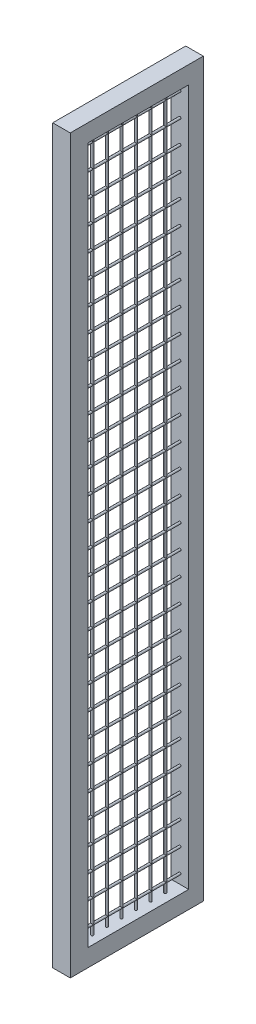
SolidWorks part; units mm, degrees
ref_plane "Piano frontale" through (0, 0, 0) normal (0, 0, 1) x (1, 0, 0)
ref_plane "Piano superiore" through (0, 0, 0) normal (0, 1, 0) x (1, 0, 0)
ref_plane "Piano destro" through (0, 0, 0) normal (1, 0, 0) x (0, 0, -1)
sketch "Schizzo1" plane through (0, 0, 1950) normal (0, 0, -1) x (-1, 0, 0)
  line L0 (-50, 2555) -> (-50, 50) construction
  line L1 (-30, 110) -> (30, 110)
  line L2 (-30, 110) -> (-30, 50)
  line L3 (-30, 50) -> (30, 50)
  line L4 (30, 110) -> (30, 50)
  line L5 (50, 2555) -> (50, 50) construction
  line L6 (-100, 50) -> (100, 50) construction
  line L7 (50, 2555) -> (-50, 2555) construction
  line L8 (-30, 2555) -> (30, 2555)
  line L9 (-30, 2555) -> (-30, 2495)
  line L10 (-30, 2495) -> (30, 2495)
  line L11 (30, 2555) -> (30, 2495)
  circle A0 centre (0, 2462.5) radius 3.75
  circle A1 centre (0, 2382.5) radius 3.75
  circle A2 centre (0, 2302.5) radius 3.75
  circle A3 centre (0, 2222.5) radius 3.75
  circle A4 centre (0, 2142.5) radius 3.75
  circle A5 centre (0, 2062.5) radius 3.75
  circle A6 centre (0, 1982.5) radius 3.75
  circle A7 centre (0, 1902.5) radius 3.75
  circle A8 centre (0, 1822.5) radius 3.75
  circle A9 centre (0, 1742.5) radius 3.75
  circle A10 centre (0, 1662.5) radius 3.75
  circle A11 centre (0, 1582.5) radius 3.75
  circle A12 centre (0, 1502.5) radius 3.75
  circle A13 centre (0, 1422.5) radius 3.75
  circle A14 centre (0, 1342.5) radius 3.75
  circle A15 centre (0, 1262.5) radius 3.75
  circle A16 centre (0, 1182.5) radius 3.75
  circle A17 centre (0, 1102.5) radius 3.75
  circle A18 centre (0, 1022.5) radius 3.75
  circle A19 centre (0, 942.5) radius 3.75
  circle A20 centre (0, 862.5) radius 3.75
  circle A21 centre (0, 782.5) radius 3.75
  circle A22 centre (0, 702.5) radius 3.75
  circle A23 centre (0, 622.5) radius 3.75
  circle A24 centre (0, 542.5) radius 3.75
  circle A25 centre (0, 462.5) radius 3.75
  circle A26 centre (0, 382.5) radius 3.75
  circle A27 centre (0, 302.5) radius 3.75
  circle A28 centre (0, 222.5) radius 3.75
  circle A29 centre (0, 142.5) radius 3.75
  dimension "D8" = 7.5
  dimension "D1" = 20
  dimension "D2" = 20
  dimension "D3" = 0
  dimension "D4" = 60
  dimension "D5" = 60
  dimension "D6" = 20
  dimension "D7" = 60
  dimension "D10" = 32.5
  dimension "D9" = 30
extrude "Estrusione-Estrusione1" add sketch "Schizzo1" along normal blind 900
sketch "Schizzo2" plane through (0, 110, 0) normal (0, 1, 0) x (1, 0, 0)
  line L1 (-30, -1050) -> (30, -1050)
  line L5 (30, -1050) -> (30, -1950) construction
  line L6 (-30, -1050) -> (-30, -1100)
  line L11 (-30, -1100) -> (30, -1100)
  line L16 (-30, -1050) -> (-30, -1950) construction
  line L17 (-30, -1950) -> (30, -1950)
  line L18 (-30, -1950) -> (-30, -1900)
  line L19 (-30, -1900) -> (30, -1900)
  line L20 (30, -1950) -> (30, -1900)
  line L21 (30, -1100) -> (30, -1050)
  line L22 (-30, -1950) -> (30, -1950) construction
  circle A44 centre (0, -1850) radius 3.75
  circle A45 centre (0, -1800) radius 3.75
  circle A46 centre (0, -1750) radius 3.75
  circle A47 centre (0, -1700) radius 3.75
  circle A48 centre (0, -1650) radius 3.75
  circle A49 centre (0, -1600) radius 3.75
  circle A50 centre (0, -1550) radius 3.75
  circle A51 centre (0, -1500) radius 3.75
  circle A52 centre (0, -1450) radius 3.75
  circle A53 centre (0, -1400) radius 3.75
  circle A54 centre (0, -1350) radius 3.75
  circle A55 centre (0, -1300) radius 3.75
  circle A56 centre (0, -1250) radius 3.75
  circle A57 centre (0, -1200) radius 3.75
  circle A58 centre (0, -1150) radius 3.75
  dimension "D3" = 50
  dimension "D5" = 15
  dimension "D1" = 50
  dimension "D2" = 60
  dimension "D8" = 0
  dimension "D4" = 50
extrude "Estrusione-Estrusione2" add sketch "Schizzo2" along normal up to surface (2385 mm away)
sketch "Schizzo3" plane through (0, 110, 0) normal (0, 1, 0) x (1, 0, 0)
  line L1 (-74.1709, -1445.2785) -> (101.082, -1445.2785)
  line L2 (-74.1709, -1445.2785) -> (-74.1709, -2075.6753)
  line L3 (-74.1709, -2075.6753) -> (101.082, -2075.6753)
  line L4 (101.082, -1445.2785) -> (101.082, -2075.6753)
  point P4 (-74.1709, -1581.6967)
  point P6 (-30, -1579.0921)
extrude "Taglio-Estrusione1" cut sketch "Schizzo3" against normal through all and the other way through all
sketch "Schizzo4" plane through (0, 2555, 0) normal (0, 1, 0) x (1, 0, 0)
  line L1 (-30, -1445.2785) -> (30, -1445.2785)
  line L2 (-30, -1445.2785) -> (-30, -1505.2785)
  line L3 (-30, -1505.2785) -> (30, -1505.2785)
  line L4 (30, -1445.2785) -> (30, -1505.2785)
extrude "Estrusione-Estrusione3" add sketch "Schizzo4" against normal up to surface (2505 mm away)
